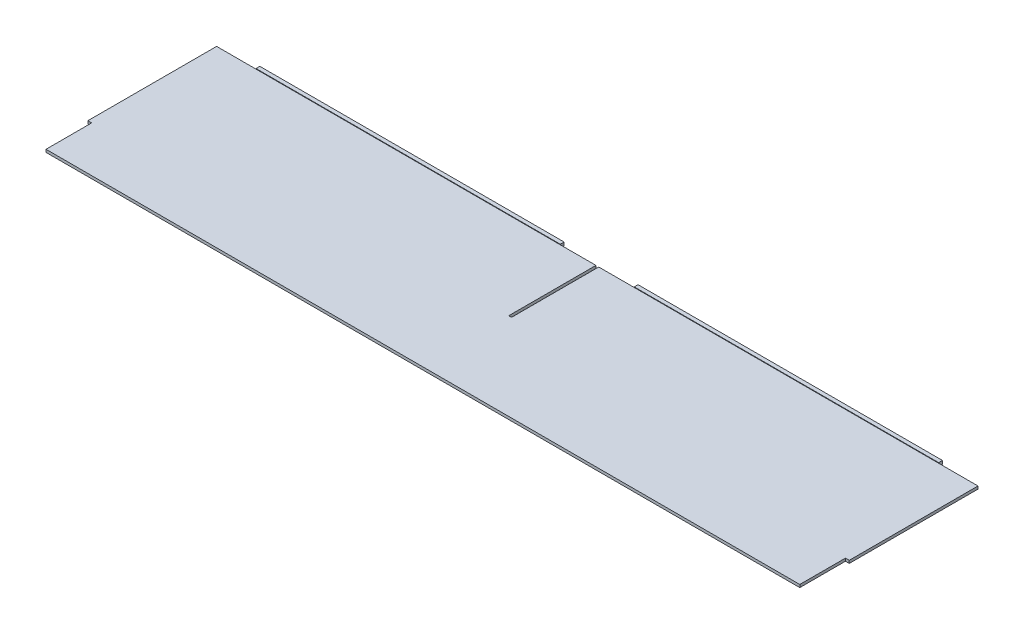
SolidWorks part; units mm, degrees
material "6061-T6 (SS)"
ref_plane "X-Y Datum" through (0, 0, 0) normal (0, 0, 1) x (1, 0, 0)
ref_plane "X-Z Datum" through (0, 0, 0) normal (0, 1, 0) x (1, 0, 0)
ref_plane "Y-Z Datum" through (0, 0, 0) normal (1, 0, 0) x (0, 0, -1)
sketch "Sketch1" plane through (0, 0, 0) normal (0, 1, 0) x (1, 0, 0)
  line L1 (-317.6778, 72.771) -> (317.6778, 72.771)
  line L2 (-317.6778, 72.771) -> (-317.6778, -72.771)
  line L3 (-317.6778, -72.771) -> (317.6778, -72.771)
  line L4 (317.6778, 72.771) -> (317.6778, -72.771)
  line L5 (-317.6778, 72.771) -> (317.6778, -72.771) construction
  line L6 (-317.6778, -72.771) -> (317.6778, 72.771) construction
  point P0 (0, 0)
  dimension "D1" = 635.3556
  dimension "D2" = 145.542
extrude "Boss-Extrude1" add sketch "Sketch1" along normal mid plane 2.286
sketch "Sketch2" plane through (0, 0, -72.771) normal (0, 0, -1) x (-1, 0, 0)
  line L20 (-317.6778, -1.143) -> (317.6778, -1.143) construction
  line L21 (-284.8229, -1.143) -> (-30.8229, -1.143)
  line L22 (30.8229, -1.143) -> (284.8229, -1.143)
  line L40 (30.8229, -1.143) -> (30.8229, 1.5875)
  line L41 (30.8229, 1.5875) -> (284.8229, 1.5875)
  line L42 (284.8229, 1.5875) -> (284.8229, -1.143)
  line L56 (-284.8229, -1.143) -> (-284.8229, 1.5875)
  line L57 (-284.8229, 1.5875) -> (-30.8229, 1.5875)
  line L58 (-30.8229, 1.5875) -> (-30.8229, -1.143)
extrude "Boss-Extrude2" add sketch "Sketch2" along normal blind 3.175
sketch "Sketch3" plane through (0, -1.143, 0) normal (0, -1, 0) x (1, 0, 0)
  line L1 (-317.6778, 72.771) -> (-314.5028, 72.771)
  line L2 (-317.6778, 72.771) -> (-317.6778, 34.671)
  line L3 (-317.6778, 34.671) -> (-314.5028, 34.671)
  line L4 (-314.5028, 72.771) -> (-314.5028, 34.671)
  dimension "D1" = 3.175
  dimension "D2" = 38.1
extrude "Cut-Extrude1" cut sketch "Sketch3" against normal through all
mirror "Mirror1" about plane through (0, 0, 0) normal (1, 0, 0) of "Cut-Extrude1"
sketch "Sketch4" plane through (0, -1.143, 0) normal (0, -1, 0) x (1, 0, 0)
  line L0 (30.8229, -72.771) -> (-30.8229, -72.771) construction
  line L1 (-1.143, -72.771) -> (1.1938, -72.771)
  line L2 (-1.143, -72.771) -> (-1.143, 0)
  line L3 (-1.143, 0) -> (1.1938, 0)
  line L4 (1.1938, -72.771) -> (1.1938, 0)
  line L5 (-1.143, -72.771) -> (-1.143, 34.671) construction
  dimension "D1" = 2.3368
  dimension "D2" = 72.771
extrude "Cut-Extrude2" cut sketch "Sketch4" against normal through all
